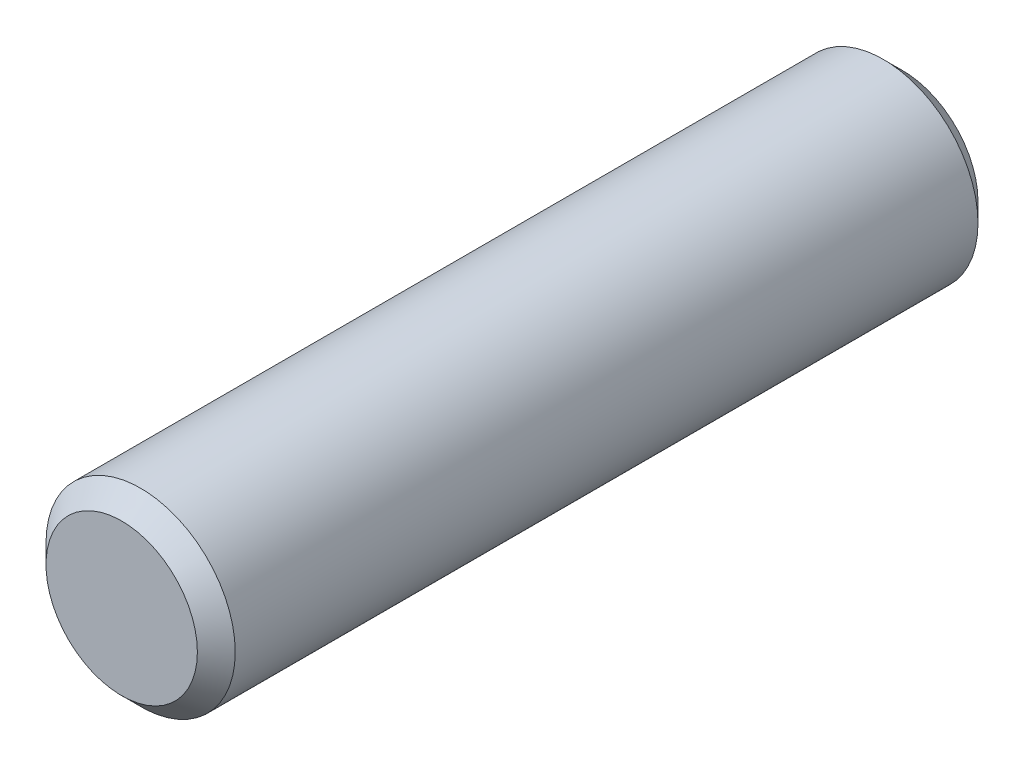
SolidWorks part; units mm, degrees
ref_plane "Front" through (0, 0, 0) normal (0, 0, 1) x (1, 0, 0)
ref_plane "Top" through (0, 0, 0) normal (0, 1, 0) x (1, 0, 0)
ref_plane "Right" through (0, 0, 0) normal (1, 0, 0) x (0, 0, -1)
sketch "Sketch1" plane through (0, 0, 0) normal (0, 0, 1) x (1, 0, 0)
  circle A0 centre (0, 0) radius 4
  dimension "dia" = 8
extrude "Extrude1" add sketch "Sketch1" along normal mid plane 33
sketch "Sketch2" plane through (0, 0, 0) normal (1, 0, 0) x (0, 0, -1)
  line L0 (16.5, 4) -> (-16.5, 4) construction
  point P0 (-16.5, 4)
  point P1 (16.5, 4)
  point P2 (-0.5, 4)
  point P5 (0.5, 4)
  dimension "D1" = 16
  dimension "D2" = 16
chamfer "Chamfer1" distance 0.8 angle 45 2 edges at (4, 0, -16.5) (4, 0, 16.5)
equation "\"D1@Chamfer1\" = \"dia@Sketch1\" * .1"
equation "\"D1@Sketch2\"=\"dia@sketch1\"*2"
equation "\"D2@Sketch2\"=\"D1@Sketch2\""
